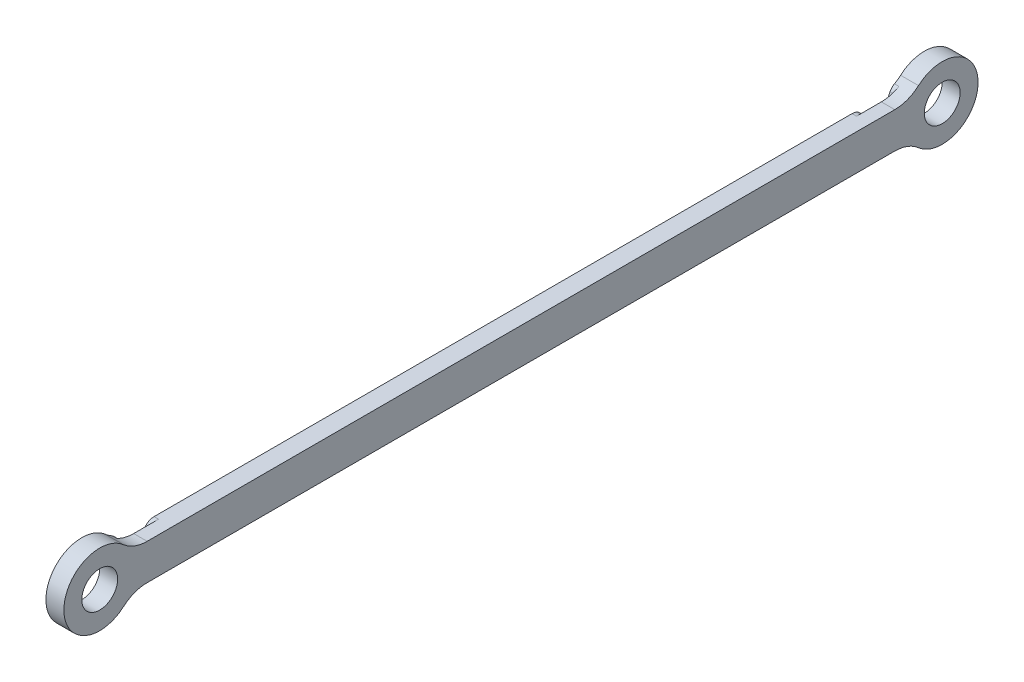
SolidWorks part; units mm, degrees
material "6061-T6 (SS)"
ref_plane "Front Plane" through (0, 0, 0) normal (0, 0, 1) x (1, 0, 0)
ref_plane "Top Plane" through (0, 0, 0) normal (0, 1, 0) x (1, 0, 0)
ref_plane "Right Plane" through (0, 0, 0) normal (1, 0, 0) x (0, 0, -1)
sketch "Sketch1" plane through (0, 0, 0) normal (1, 0, 0) x (0, 0, -1)
  line L0 (0, 0) -> (149.225, 0) construction
  line L1 (0, 3.175) -> (149.225, 3.175)
  line L2 (0, -3.175) -> (149.225, -3.175)
  arc A0 (0, 3.175) -> (0, -3.175) centre (0, 0) ccw
  arc A1 (149.225, -3.175) -> (149.225, 3.175) centre (149.225, 0) ccw
  circle A2 centre (0, 0) radius 3.175
  circle A3 centre (149.225, 0) radius 3.175
  circle A4 centre (0, 0) radius 6.35
  circle A5 centre (149.225, 0) radius 6.35
  point P3 (74.6125, 0)
  point P14 (0, 0)
  point P15 (0, 0)
  dimension "D1" = 6.35
  dimension "D3" = 12.7
  dimension "D2" = 6.35
  dimension "D4" = 149.225
extrude "Boss-Extrude1" add sketch "Sketch1" along normal mid plane 3.175 contours A4 L0 A5 L1 | L0 A4 L2 A5 | L1 A4 L2 A2 | A2 L0 A4 L1 | L0 A2 L2 A4 | L2 A5 L1 A3 | A5 L0 A3 L1 | L0 A5 L2 A3
fillet "Fillet1" radius 6.35 4 edges at (0, 3.175, -143.7257) (0, -3.175, -143.7257) (0, -3.175, -5.4993) (0, 3.175, -5.4993)
sketch "Sketch2" plane through (-1.5875, 0, 0) normal (-1, 0, 0) x (0, 0, 1)
  line L0 (-8.4003, -3.175) -> (-140.8247, -3.175) construction
  line L1 (-8.4003, 3.175) -> (-140.8247, 3.175) construction
  line L2 (-8.4003, -3.175) -> (-140.8247, -3.175)
  line L3 (-8.4003, 3.175) -> (-140.8247, 3.175)
  arc A0 (-5.7342, -3.7618) -> (-5.7342, 3.7618) centre (0, 0) cw
  arc A1 (-4.2001, -4.7625) -> (-8.4003, -3.175) centre (-8.4003, -9.525) ccw construction
  arc A2 (-8.4003, 3.175) -> (-4.2001, 4.7625) centre (-8.4003, 9.525) ccw construction
  arc A3 (-10.3834, -3.175) -> (-10.3834, 3.175) centre (0, 0) cw
  arc A4 (-4.2001, -4.7625) -> (-8.4003, -3.175) centre (-8.4003, -9.525) ccw
  arc A5 (-8.4003, 3.175) -> (-4.2001, 4.7625) centre (-8.4003, 9.525) ccw
  arc A6 (-4.2001, -4.7625) -> (-4.2001, 4.7625) centre (0, 0) ccw construction
  point P15 (-8.8965, -3.175)
  point P18 (-8.9803, 3.175)
  arc M2 (-4.2001, 4.7625) -> (-8.4003, 3.175) centre (-8.4003, 9.525) cw
  arc M8 (-8.4003, -3.175) -> (-4.2001, -4.7625) centre (-8.4003, -9.525) cw
  dimension "D1" = 0.508
  dimension "D2" = 4
extrude "Cut-Extrude1" cut sketch "Sketch2" against normal blind 0.7937 contours A3 A0 M8 M2
ref_plane "Plane1" through (0, 0, -74.6125) normal (0, 0, 1) x (1, 0, 0)
mirror "Mirror1" about plane through (0, 0, -74.6125) normal (0, 0, 1) of "Cut-Extrude1"
fillet "Fillet2" radius 2 8 edges at (-1.1906, 3.7618, -5.7342) (-1.1906, -3.7618, -5.7342) (-1.1906, -3.175, -10.3834) (-1.1906, 3.175, -10.3834) (-1.1906, -3.175, -138.8416) (-1.1906, 3.7618, -143.4908) (-1.1906, 3.175, -138.8416) (-1.1906, -3.7618, -143.4908)
equation "\"D2@Sketch2\"=4mm"
